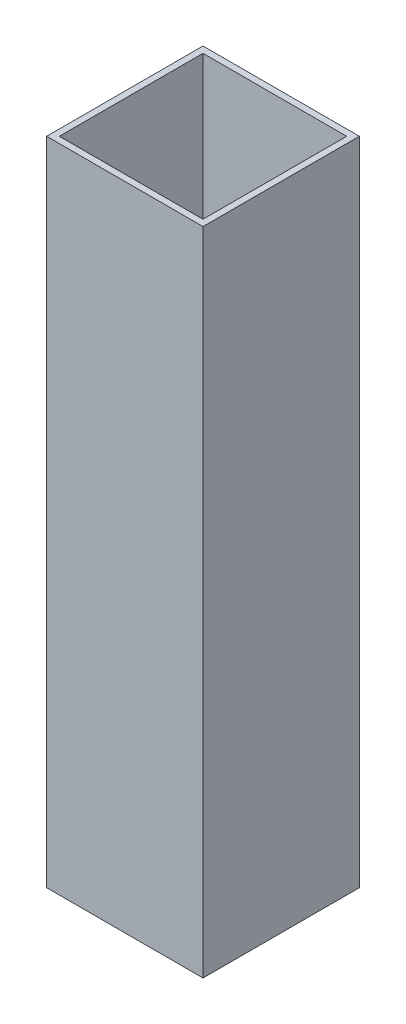
SolidWorks part; units mm, degrees
ref_plane "Front Plane" through (0, 0, 0) normal (0, 0, 1) x (1, 0, 0)
ref_plane "Top Plane" through (0, 0, 0) normal (0, 1, 0) x (1, 0, 0)
ref_plane "Right Plane" through (0, 0, 0) normal (1, 0, 0) x (0, 0, -1)
sketch "Sketch1" plane through (0, 0, 0) normal (0, 1, 0) x (1, 0, 0)
  line L0 (-9.398, -9.398) -> (-9.398, 9.398)
  line L1 (-8.636, -8.636) -> (8.636, -8.636)
  line L2 (-8.636, -8.636) -> (-8.636, 8.636)
  line L3 (-8.636, 8.636) -> (8.636, 8.636)
  line L4 (8.636, -8.636) -> (8.636, 8.636)
  line L5 (-8.636, -8.636) -> (8.636, 8.636) construction
  line L6 (-8.636, 8.636) -> (8.636, -8.636) construction
  line L7 (-9.398, 9.398) -> (9.398, 9.398)
  line L8 (9.398, -9.398) -> (9.398, 9.398)
  line L9 (-9.398, -9.398) -> (9.398, -9.398)
  point P0 (0, 0)
  dimension "D1" = 17.272
  dimension "D2" = 0.762
extrude "Boss-Extrude1" add sketch "Sketch1" along normal blind 76.2 contours L0 L9 L8 L7 L4 L1 L2 L3
sketch "Sketch2" plane through (0, 0, 0) normal (0, -1, 0) x (1, 0, 0)
  line L0 (9.398, 9.398) -> (9.398, -9.398) construction
  line L1 (-9.398, -9.398) -> (9.398, -9.398) construction
  line L2 (-9.398, 9.398) -> (-9.398, -9.398) construction
  line L3 (-9.398, 9.398) -> (9.398, 9.398) construction
  line L4 (9.398, 9.398) -> (9.398, -9.398)
  line L5 (-9.398, -9.398) -> (9.398, -9.398)
  line L6 (-9.398, 9.398) -> (-9.398, -9.398)
  line L7 (-9.398, 9.398) -> (9.398, 9.398)
extrude "Boss-Extrude2" add sketch "Sketch2" along normal blind 2.032
hole_wizard "#10 (0.1935) Diameter Hole1" positions "Sketch3" profile "Sketch4" hole size "#10" standard "ANSI Inch"
sketch "Sketch3" plane through (0, -2.032, 0) normal (0, -1, 0) x (-1, 0, 0)
  point P0 (0, 0)
sketch "Sketch4" plane through (0, -2.032, 0) normal (1, 0, 0) x (0, 0, -1)
  line L0 (0, 0) -> (0, 7.7236)
  line L1 (0, 7.7236) -> (2.286, 6.35)
  line L2 (2.286, 6.35) -> (2.286, 0)
  line L5 (2.286, 0) -> (0, 0)
  line L10 (0, 7.7236) -> (-2.286, 6.35) construction
  line L11 (0, -6.35) -> (0, 107.95) construction
  dimension "Hole Dia." = 4.572
  dimension "Hole Depth" = 6.35
  dimension "Drill Angle" = 118
